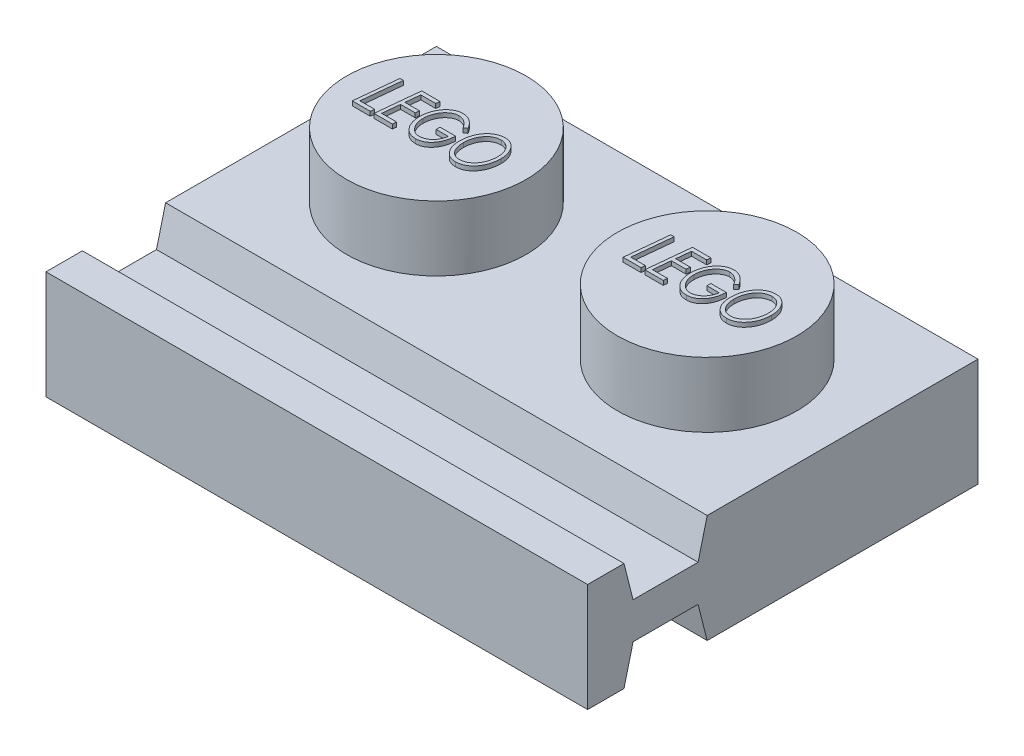
SolidWorks part; units mm, degrees
ref_plane "Front Plane" through (0, 0, 0) normal (0, 0, 1) x (1, 0, 0)
ref_plane "Top Plane" through (0, 0, 0) normal (0, 1, 0) x (1, 0, 0)
ref_plane "Right Plane" through (0, 0, 0) normal (1, 0, 0) x (0, 0, -1)
sketch "Sketch2" plane through (0, 0, 0) normal (0, 1, 0) x (1, 0, 0)
  line L0 (-17.7331, 8.7234) -> (-1.8581, 8.7234)
  line L1 (-1.8581, 8.7234) -> (-1.8581, 0.7859)
  line L2 (-1.8581, 0.7859) -> (-17.7331, 0.7859)
  line L3 (-17.7331, 0.7859) -> (-17.7331, 8.7234)
  dimension "D1" = 15.875
  dimension "D2" = 7.9375
extrude "Boss-Extrude3" add sketch "Sketch2" along normal blind 3.175
sketch "Sketch3" plane through (0, 3.175, 0) normal (0, 1, 0) x (1, 0, 0)
  line L0 (-17.7331, 8.7234) -> (-17.7331, 0.7859) construction
  line L1 (-1.8581, 8.7234) -> (-17.7331, 8.7234) construction
  circle A0 centre (-13.7644, 4.7546) radius 2.6308
  dimension "D1" = 3.9687
  dimension "D2" = 3.9688
extrude "Boss-Extrude4" add sketch "Sketch3" along normal blind 1.905
pattern_linear "LPattern1" count 2 spacing 7.9375 along (1, 0, 0) of "Boss-Extrude4"
shell "Shell1" thickness 1.524
sketch "Sketch4" plane through (0, 5.08, 0) normal (0, 1, 0) x (1, 0, 0)
  line L1 (-13.7644, 4.7546) -> (-13.7644, 4.0766) construction
  line L2 (-15.584, 4.0766) -> (-11.9447, 4.0766) construction
  text T0 "<i>LEGO</i>" font "Century Gothic" height 1.27
  point P4 (-13.7644, 4.7546)
  point P9 (-13.7644, 4.0766)
extrude "Boss-Extrude5" add sketch "Sketch4" along normal blind 0.127
pattern_linear "LPattern2" count 2 spacing 7.9375 along (1, 0, 0) of "Boss-Extrude5"
sketch "Sketch5" plane through (0, 0, 0) normal (0, -1, 0) x (1, 0, 0)
  circle A0 centre (-9.7956, -4.7546) radius 1.4986
  circle A1 centre (-9.7956, -4.7546) radius 0.635
  dimension "D1" = 2.9972
  dimension "D2" = 1.27
extrude "Boss-Extrude6" add sketch "Sketch5" against normal up to surface (1.651 mm away) up to face at (-5.8269, 1.651, -5.8614)
sketch "Sketch6" plane through (-1.8581, 0, 0) normal (1, 0, 0) x (0, 0, -1)
  line L0 (0.7859, 3.175) -> (0.7859, 0)
  line L1 (0.7859, 1.5875) -> (-2.7193, 1.5875) construction
  line L2 (-2.7193, 3.175) -> (-2.7193, 0)
  line L3 (-2.7193, 0) -> (-1.6525, 0)
  line L4 (-1.6525, 0) -> (-1.3858, 1.0541)
  line L5 (-1.3858, 1.0541) -> (0.5192, 1.0541)
  line L6 (0.5192, 1.0541) -> (0.7859, 0)
  line L7 (0.7859, 0) -> (-1.6525, 0) construction
  line L8 (-0.4333, 0) -> (-0.4333, 2.0174) construction
  line L9 (0.5192, 2.1209) -> (0.7859, 3.175)
  line L10 (-1.3858, 2.1209) -> (0.5192, 2.1209)
  line L11 (-1.6525, 3.175) -> (-1.3858, 2.1209)
  line L12 (-2.7193, 3.175) -> (-1.6525, 3.175)
  point P13 (-0.4333, 1.0541)
  dimension "D1" = 1.905
  dimension "D2" = 3.5052
  dimension "D3" = 2.4384
extrude "Boss-Extrude7" add sketch "Sketch6" against normal up to surface (15.875 mm away) up to face at (-17.7331, 1.5875, -4.7546)
